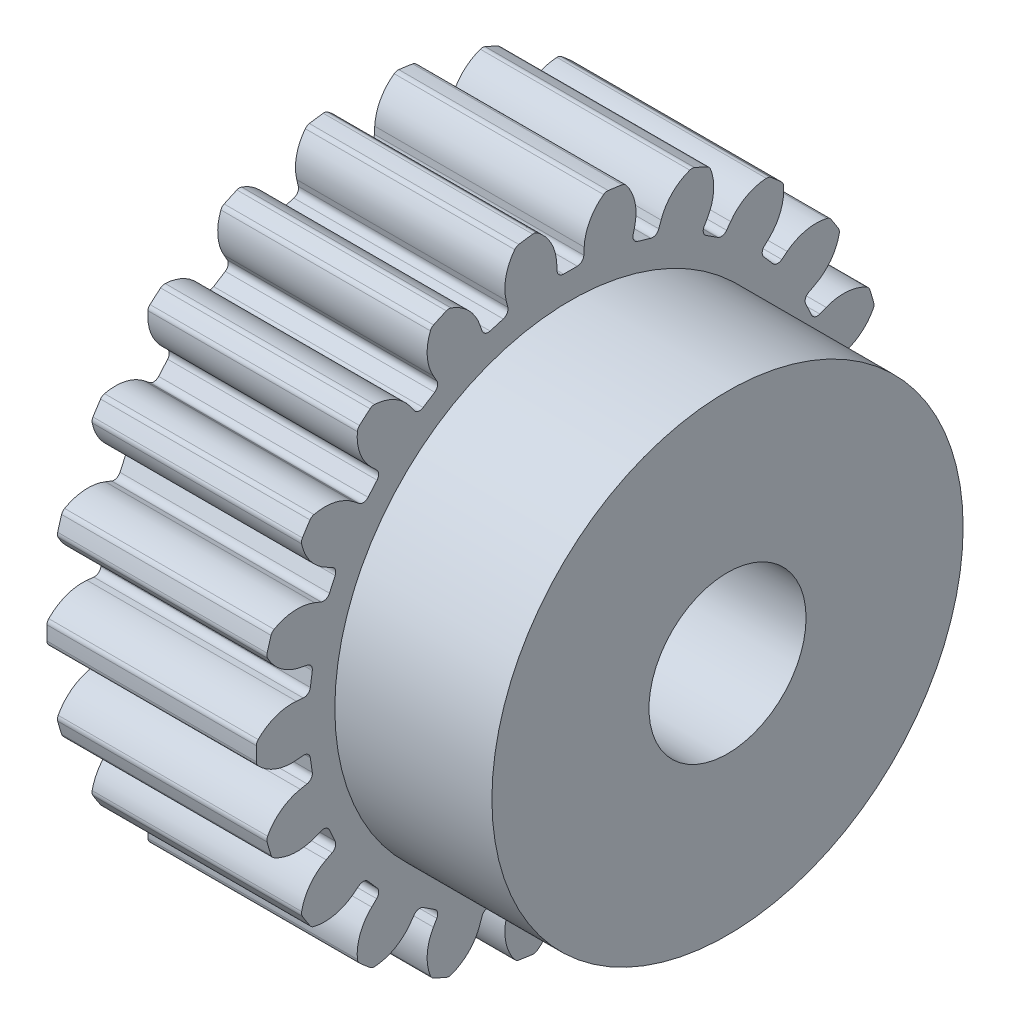
SolidWorks part; units mm, degrees
ref_plane "Plan de face" through (0, 0, 0) normal (0, 0, 1) x (1, 0, 0)
ref_plane "Plan de dessus" through (0, 0, 0) normal (0, 1, 0) x (1, 0, 0)
ref_plane "Plan de droite" through (0, 0, 0) normal (1, 0, 0) x (0, 0, -1)
sketch "Esquisse1" plane through (0, 0, 0) normal (1, 0, 0) x (0, 0, -1)
  circle A0 centre (0, 0) radius 12
  circle A1 centre (0, 0) radius 3
  dimension "D1" = 24
  dimension "D2" = 6
extrude "Extrusion1" add sketch "Esquisse1" along normal blind 8
sketch "Esquisse22" plane through (0, 0, 0) normal (-1, 0, 0) x (0, 0, 1)
  line L0 (0, 0) -> (0, 12) construction
  line L1 (-0.5, 10) -> (0.5, 10)
  line L2 (0.5, 10) -> (0.525, 10.5)
  line L3 (0, 0) -> (-0.5, 10) construction
  line L4 (-0.5, 10) -> (-0.525, 10.5)
  line L6 (-0.525, 10.5) -> (0, 10.5) construction
  line L7 (-0.525, 10.5) -> (-0.5993, 11.985) construction
  circle A0 centre (0, 0) radius 12 construction
  arc A1 (-0.525, 10.5) -> (-1.3493, 11.9239) centre (-2.3223, 10.4101) ccw
  arc A2 (-1.3493, 11.9239) -> (1.3493, 11.9239) centre (0, 0) cw
  arc A3 (0.525, 10.5) -> (1.3493, 11.9239) centre (2.3223, 10.4101) cw
  point P13 (0, 10)
  dimension "D1" = 0.75
  dimension "D2" = 0.5
  dimension "D3" = 2
  dimension "D4" = 180
  dimension "D6" = 0.5
extrude "Enlèv. mat.-Extru.2" cut sketch "Esquisse22" against normal up to next (8 mm away)
fillet "Congé2" radius 0.25 4 edges at (4, 11.9239, 1.3493) (4, 10, 0.5) (4, 10, -0.5) (4, 11.9239, -1.3493)
pattern_circular "Répétition circulaire1" count 22 over 360 about axis through (0, 0, 0) along (1, 0, 0) of "Enlèv. mat.-Extru.2", "Congé2"
sketch "Esquisse23" plane through (8, 0, 0) normal (1, 0, 0) x (0, 0, -1)
  circle A0 centre (0, 0) radius 3
  circle A1 centre (0, 0) radius 9
  circle A2 centre (0, 0) radius 3 construction
  dimension "D1" = 18
extrude "Extrusion2" add sketch "Esquisse23" along normal blind 6
